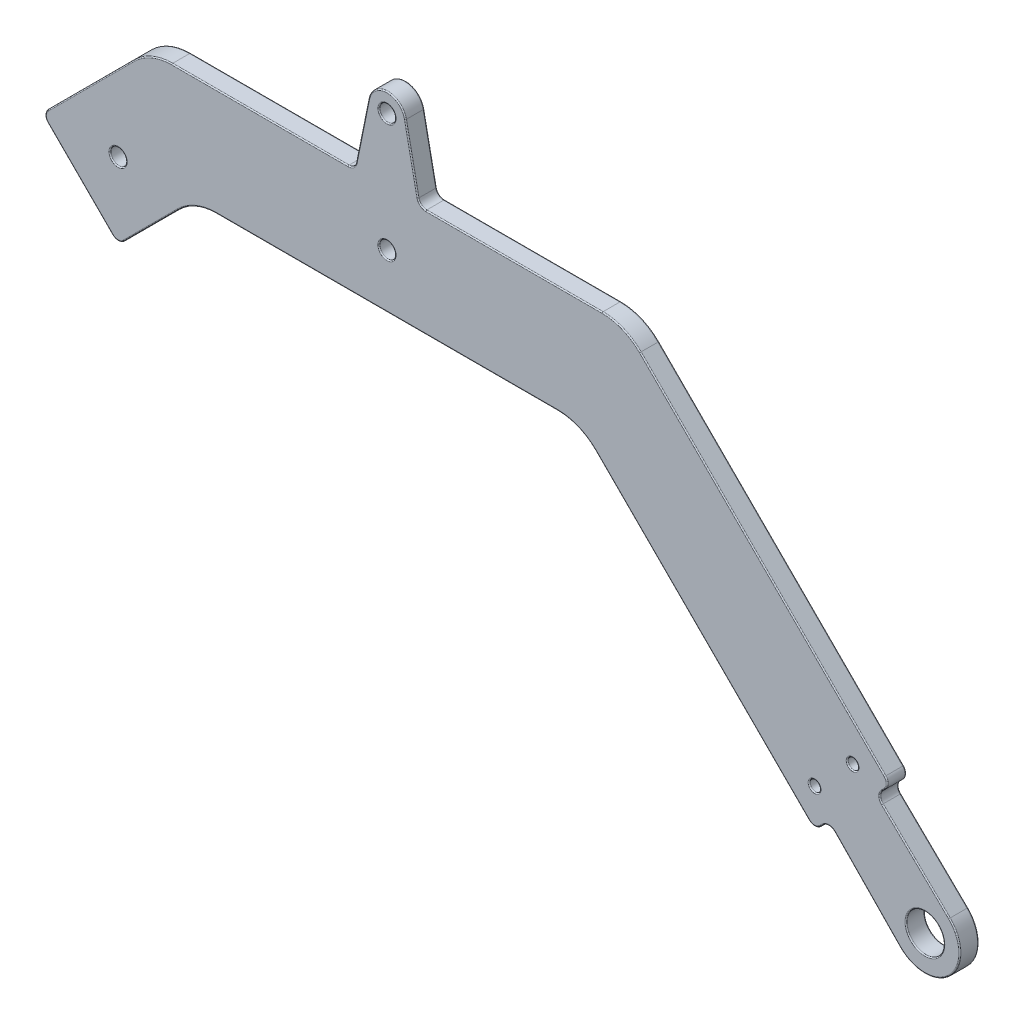
SolidWorks part; units mm, degrees
ref_plane "Front Plane" through (0, 0, 0) normal (0, 0, 1) x (1, 0, 0)
ref_plane "Top Plane" through (0, 0, 0) normal (0, 1, 0) x (1, 0, 0)
ref_plane "Right Plane" through (0, 0, 0) normal (1, 0, 0) x (0, 0, -1)
sketch "Sketch1" plane through (0, 0, 0) normal (0, 0, 1) x (1, 0, 0)
  line L0 (-100, 0) -> (100, 0) construction
  line L1 (-100, 0) -> (0, 100) construction
  line L2 (0, 100) -> (100, 0) construction
  line L3 (0, 0) -> (-50, 50) construction
  line L4 (-40, 60) -> (40, 60) construction
  line L5 (0, 100) -> (0, 60) construction
  circle A0 centre (-100, 0) radius 20
  circle A1 centre (0, 0) radius 20
  circle A2 centre (100, 0) radius 20
  point P2 (0, 0)
  point P13 (0, 0)
  dimension "D5" = 40
  dimension "D1" = 200
  dimension "D2" = 90
  dimension "D3" = 90
  dimension "D4" = 80
sketch "Sketch2" plane through (0, 0, 0) normal (0, 0, 1) x (1, 0, 0)
  line L0 (93.636, 20.5061) -> (79.4939, 6.364)
  line L1 (90.9809, 17.8509) -> (104.534, 4.6576)
  line L2 (-57.0711, 42.9289) -> (-40, 60) construction
  line L3 (-100, 0) -> (0, 100) construction
  line L4 (-40, 60) -> (40, 60) construction
  line L5 (40, 60) -> (86.565, 13.435) construction
  line L6 (0, 100) -> (100, 0) construction
  line L7 (-50, 35.8579) -> (-35.8579, 50)
  line L8 (-35.8579, 50) -> (35.8579, 50)
  line L9 (35.8579, 50) -> (79.4939, 6.364)
  line L10 (-64.1421, 50) -> (-44.1421, 70)
  line L11 (-44.1421, 70) -> (44.1421, 70)
  line L12 (44.1421, 70) -> (93.636, 20.5061)
  line L13 (-64.1421, 50) -> (-50, 35.8579)
  line L14 (82.1491, 9.0191) -> (95.3424, -4.534)
  line L15 (90.1005, 24.0416) -> (75.9584, 9.8995) construction
  line L17 (0, 100) -> (0, 60) construction
  line L18 (6, 70) -> (3.4304, 82.6944)
  line L19 (-6, 70) -> (-3.4304, 82.6944)
  circle A0 centre (100, 0) radius 3.5
  circle A1 centre (100, 0) radius 10 construction
  arc A2 (95.3424, -4.534) -> (104.534, 4.6576) centre (100, 0) ccw
  circle A3 centre (100, 0) radius 20 construction
  circle A4 centre (100, 0) radius 6.5 construction
  circle A5 centre (86.565, 20.5061) radius 1
  circle A6 centre (79.4939, 13.435) radius 1
  circle A7 centre (0, 60) radius 1.5
  circle A9 centre (0, 82) radius 1.5
  arc A10 (3.4304, 82.6944) -> (-3.4304, 82.6944) centre (0, 82) ccw
  circle A11 centre (0, 82) radius 3.5 construction
  circle A13 centre (-50, 50) radius 1.5
  point P44 (0, 0)
  point P49 (0, 0)
  dimension "D4" = 20
  dimension "D5" = 7
  dimension "D9" = 2
  dimension "D12" = 3
  dimension "D18" = 3
  dimension "D3" = 20
  dimension "D7" = 19
  dimension "D8" = 5
  dimension "D10" = 5
  dimension "D11" = 5
  dimension "D13" = 12
  dimension "D15" = 6
  dimension "D16" = 6
  dimension "D1" = 10
  dimension "D2" = 10
  dimension "D6" = 3
  dimension "D14" = 2
sketch "Sketch3" plane through (0, 0, 0) normal (0, 0, 1) x (1, 0, 0)
  line L0 (-86.565, 13.435) -> (-50, 50) construction
  line L1 (-100, 0) -> (0, 100) construction
  line L2 (-50, 50) -> (-13.435, 13.435) construction
  line L3 (0, 0) -> (-50, 50) construction
  line L4 (-79.4939, 6.364) -> (-50, 35.8579)
  line L5 (-50, 35.8579) -> (-20.5061, 6.364)
  line L6 (-93.636, 20.5061) -> (-50, 64.1421)
  line L7 (-50, 64.1421) -> (-6.364, 20.5061)
  line L8 (-79.4939, 6.364) -> (-50, 35.8579) construction
  line L9 (-93.636, 20.5061) -> (-50, 64.1421) construction
  line L10 (-93.636, 20.5061) -> (-79.4939, 6.364)
  line L11 (-6.364, 20.5061) -> (-20.5061, 6.364)
  line L12 (-104.534, 4.6576) -> (-90.9809, 17.8509)
  line L13 (-95.4038, -4.5962) -> (-81.9688, 8.8388)
  line L14 (4.5962, 4.5962) -> (-8.8388, 18.0312)
  line L15 (-4.5962, -4.5962) -> (-18.0312, 8.8388)
  line L16 (-90.1005, 24.0416) -> (-75.9584, 9.8995) construction
  line L17 (-9.8995, 24.0416) -> (-24.0416, 9.8995) construction
  circle A0 centre (-100, 0) radius 3.5
  circle A1 centre (0, 0) radius 3.5
  circle A2 centre (-100, 0) radius 10 construction
  circle A3 centre (0, 0) radius 10 construction
  arc A4 (-104.534, 4.6576) -> (-95.4038, -4.5962) centre (-100, 0) ccw
  arc A5 (-4.5962, -4.5962) -> (4.5962, 4.5962) centre (0, 0) ccw
  circle A6 centre (-100, 0) radius 20 construction
  circle A7 centre (-100, 0) radius 6.5 construction
  circle A8 centre (0, 0) radius 6.5 construction
  circle A9 centre (-86.565, 20.5061) radius 1
  circle A10 centre (-79.4939, 13.435) radius 1
  circle A11 centre (-20.5061, 13.435) radius 1
  circle A12 centre (-13.435, 20.5061) radius 1
  circle A13 centre (-50, 50) radius 1.5 construction
  circle A14 centre (-50, 50) radius 1.5
  dimension "D1" = 7
  dimension "D2" = 20
  dimension "D3" = 3
  dimension "D8" = 2
  dimension "D6" = 19
  dimension "D7" = 19
  dimension "D9" = 5
  dimension "D10" = 5
  dimension "D11" = 5
  dimension "D12" = 5
  dimension "D13" = 5
  dimension "D14" = 5
  dimension "D4" = 10
  dimension "D5" = 10
sketch "Sketch5" plane through (0, 0, 0) normal (0, 0, 1) x (1, 0, 0)
  line L6 (4, 60) -> (4, 70)
  line L7 (-4, 60) -> (-4, 70)
  line L10 (-57.5, 93.3579) -> (57.5, 93.3579)
  line L11 (57.5, 93.3579) -> (57.5, 83.3579)
  line L12 (57.5, 83.3579) -> (44.1421, 70)
  line L13 (44.1421, 70) -> (-44.1421, 70)
  line L14 (-44.1421, 70) -> (-57.5, 83.3579)
  line L15 (-57.5, 83.3579) -> (-57.5, 93.3579)
  line L16 (-22.5, 84.8579) -> (22.5, 84.8579) construction
  line L17 (-22.5, 89.3579) -> (22.5, 89.3579)
  line L18 (-22.5, 80.3579) -> (22.5, 80.3579)
  circle A0 centre (0, 60) radius 1.5 construction
  circle A1 centre (0, 60) radius 1.5
  arc A2 (-4, 60) -> (4, 60) centre (0, 60) ccw
  circle A3 centre (0, 60) radius 4 construction
  arc A4 (-22.5, 89.3579) -> (-22.5, 80.3579) centre (-22.5, 84.8579) ccw
  arc A5 (22.5, 80.3579) -> (22.5, 89.3579) centre (22.5, 84.8579) ccw
  point P2 (0, 93.3579)
  point P7 (0, 84.8579)
  point P26 (0, 0)
  point P27 (0, 0)
  point P28 (0, 0)
  point P29 (0, 0)
  dimension "D1" = 115
  dimension "D2" = 10
  dimension "D3" = 2.5
  dimension "D4" = 45
  dimension "D5" = 9
  dimension "D6" = 4
sketch "Sketch6" plane through (0, 0, 0) normal (0, 0, 1) x (1, 0, 0)
sketch "Sketch7" plane through (0, 0, 0) normal (0, 0, 1) x (1, 0, 0)
  line L0 (90.9809, 17.8509) -> (104.534, 4.6576) construction
  line L1 (82.1491, 9.0191) -> (95.3424, -4.534) construction
  line L2 (-6, 70) -> (-3.4304, 82.6944) construction
  line L3 (6, 70) -> (3.4304, 82.6944) construction
  line L4 (90.9809, 17.8509) -> (104.534, 4.6576)
  line L5 (82.1491, 9.0191) -> (95.3424, -4.534)
  line L6 (-6, 70) -> (-3.4304, 82.6944)
  line L7 (6, 70) -> (3.4304, 82.6944)
  line L8 (79.4939, 6.364) -> (93.636, 20.5061)
  line L9 (35.8579, 50) -> (79.4939, 6.364)
  line L10 (-35.8579, 50) -> (35.8579, 50)
  line L11 (-50, 35.8579) -> (-35.8579, 50)
  line L12 (-64.1421, 50) -> (-50, 35.8579)
  line L13 (-44.1421, 70) -> (-64.1421, 50)
  line L14 (44.1421, 70) -> (-44.1421, 70)
  line L15 (93.636, 20.5061) -> (44.1421, 70)
  line L16 (79.4939, 6.364) -> (82.1491, 9.0191)
  line L17 (35.8579, 50) -> (79.4939, 6.364)
  line L18 (-35.8579, 50) -> (35.8579, 50)
  line L19 (-50, 35.8579) -> (-35.8579, 50)
  line L20 (-64.1421, 50) -> (-50, 35.8579)
  line L21 (-44.1421, 70) -> (-64.1421, 50)
  line L22 (44.1421, 70) -> (6, 70)
  line L23 (93.636, 20.5061) -> (44.1421, 70)
  line L24 (-6, 70) -> (-44.1421, 70)
  line L25 (90.9809, 17.8509) -> (93.636, 20.5061)
  arc A0 (95.3424, -4.534) -> (104.534, 4.6576) centre (100, 0) ccw construction
  circle A1 centre (86.565, 20.5061) radius 1
  circle A2 centre (86.565, 20.5061) radius 1
  circle A3 centre (100, 0) radius 3.5
  circle A4 centre (100, 0) radius 3.5
  circle A5 centre (0, 82) radius 1.5
  circle A6 centre (0, 82) radius 1.5
  circle A7 centre (0, 60) radius 1.5
  circle A8 centre (0, 60) radius 1.5
  circle A9 centre (79.4939, 13.435) radius 1
  circle A10 centre (79.4939, 13.435) radius 1
  circle A11 centre (-50, 50) radius 1.5
  circle A12 centre (-50, 50) radius 1.5
  arc A13 (3.4304, 82.6944) -> (-3.4304, 82.6944) centre (0, 82) ccw construction
  arc A14 (95.3424, -4.534) -> (104.534, 4.6576) centre (100, 0) ccw
  arc A15 (3.4304, 82.6944) -> (-3.4304, 82.6944) centre (0, 82) ccw
  dimension "D1" = 0
  dimension "D2" = 0
  dimension "D3" = 0
  dimension "D4" = 0
  dimension "D5" = 0
  dimension "D6" = 0
  dimension "D7" = 0
extrude "Boss-Extrude1" add sketch "Sketch7" along normal blind 3.5
fillet "Fillet1" radius 10 4 edges at (-35.8579, 50, 1.75) (35.8579, 50, 1.75) (-44.1421, 70, 1.75) (44.1421, 70, 1.75)
fillet "Fillet2" radius 1.5 8 edges at (-50, 35.8579, 1.75) (-64.1421, 50, 1.75) (-6, 70, 1.75) (6, 70, 1.75) (90.9809, 17.8509, 1.75) (93.636, 20.5061, 1.75) (79.4939, 6.364, 1.75) (82.1491, 9.0191, 1.75)
fillet "Fillet3" radius 0.2 68 edges at (-48.5, 50, 0) (-48.5, 50, 3.5) (80.4939, 13.435, 0) (80.4939, 13.435, 3.5) (1.5, 60, 0) (1.5, 60, 3.5) (1.5, 82, 0) (1.5, 82, 3.5) (103.5, 0, 0) (103.5, 0, 3.5) (87.565, 20.5061, 0) (87.565, 20.5061, 3.5) (92.3156, 19.1857, 0) (69.8232, 44.3189, 0) (23.6134, 70, 0) (4.5935, 76.9484, 0) (0, 85.5, 0) (-4.5935, 76.9484, 0) (-23.6134, 70, 0) (-55.0763, 59.0659, 0) (-57.0711, 42.9289, 0) (-43.8631, 41.9948, 0) (0, 50, 0) (58.61, 27.2478, 0) (80.8143, 7.6844, 0) (89.276, 1.6979, 0) (104.5962, -4.5962, 0) (98.3021, 10.724, 0) (92.3156, 19.1857, 3.5) (69.8232, 44.3189, 3.5) (4.5935, 76.9484, 3.5) (0, 85.5, 3.5) (-4.5935, 76.9484, 3.5) (-23.6134, 70, 3.5) (-55.0763, 59.0659, 3.5) (-57.0711, 42.9289, 3.5) (-43.8631, 41.9948, 3.5) (0, 50, 3.5) (58.61, 27.2478, 3.5) (80.8143, 7.6844, 3.5) (89.276, 1.6979, 3.5) (104.5962, -4.5962, 3.5) (98.3021, 10.724, 3.5) (43.8268, 69.2388, 0) (-43.8268, 69.2388, 0) (43.8268, 69.2388, 3.5) (-43.8268, 69.2388, 3.5) (-35.5426, 49.2388, 0) (-35.5426, 49.2388, 3.5) (35.5426, 49.2388, 0) (35.5426, 49.2388, 3.5) (79.4939, 6.9853, 0) (93.0147, 20.5061, 0) (-63.5208, 50, 0) (-50, 36.4792, 0) (79.4939, 6.9853, 3.5) (93.0147, 20.5061, 3.5) (-63.5208, 50, 3.5) (-50, 36.4792, 3.5) (-6.2772, 70.3389, 0) (-6.2772, 70.3389, 3.5) (6.2772, 70.3389, 0) (6.2772, 70.3389, 3.5) (91.6166, 17.8552, 0) (91.6166, 17.8552, 3.5) (82.1448, 8.3834, 0) (82.1448, 8.3834, 3.5) (23.6134, 70, 3.5)
